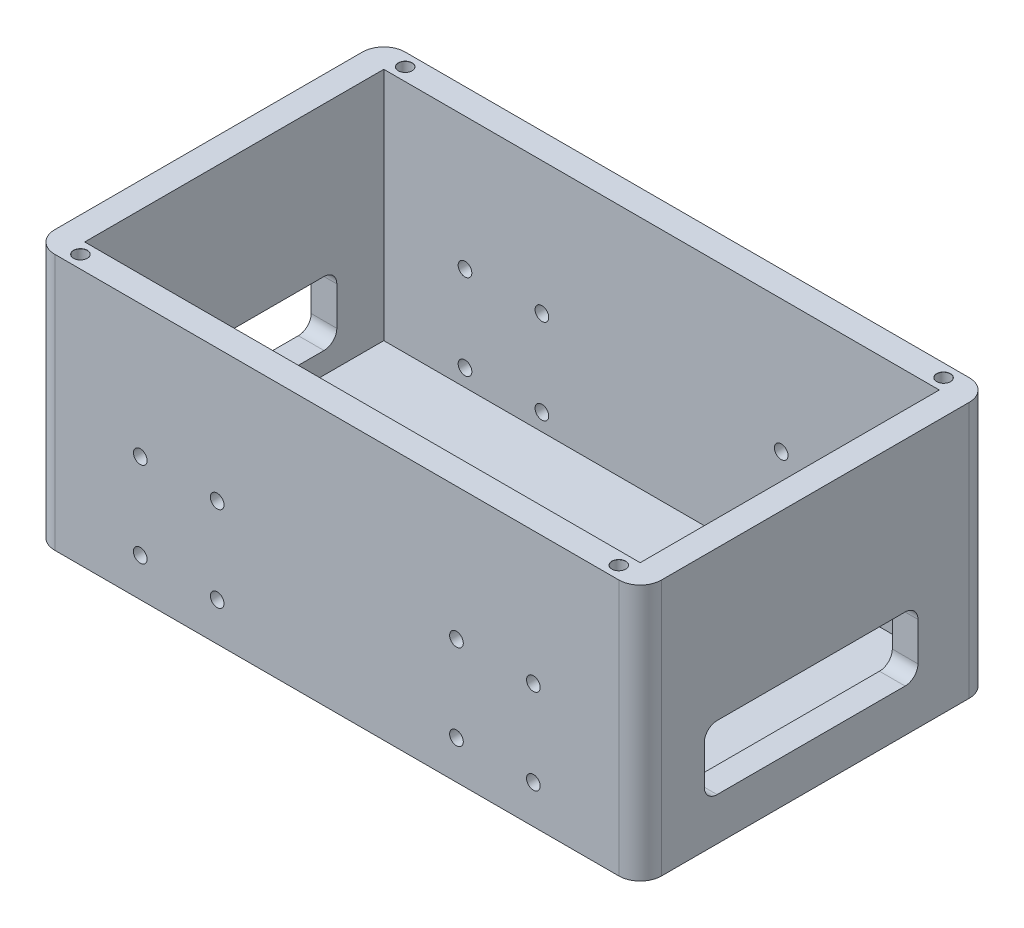
SolidWorks part; units mm, degrees
ref_plane "前视基准面" through (0, 0, 0) normal (0, 0, 1) x (1, 0, 0)
ref_plane "上视基准面" through (0, 0, 0) normal (0, 1, 0) x (1, 0, 0)
ref_plane "右视基准面" through (0, 0, 0) normal (1, 0, 0) x (0, 0, -1)
sketch "Sketch1" plane through (0, 0, 0) normal (0, 1, 0) x (1, 0, 0)
  line L1 (0, 0) -> (142, 0)
  line L2 (0, 0) -> (0, -82)
  line L3 (0, -82) -> (142, -82)
  line L4 (142, 0) -> (142, -82)
  dimension "D1" = 142
  dimension "D2" = 82
extrude "Boss-Extrude1" add sketch "Sketch1" along normal blind 60 contours L2 L1 L4 L3
sketch "Sketch2" plane through (0, 60, 0) normal (0, 1, 0) x (1, 0, 0)
  line L0 (0, -82) -> (142, -82) construction
  line L1 (6, -76) -> (136, -76)
  line L2 (6, -76) -> (6, -6)
  line L3 (6, -6) -> (136, -6)
  line L4 (136, -76) -> (136, -6)
  line L5 (6, -76) -> (136, -6) construction
  line L6 (6, -6) -> (136, -76) construction
  line L7 (142, 0) -> (142, -82) construction
  point P0 (71, -41)
  dimension "D1" = 130
  dimension "D2" = 70
  dimension "D3" = 6
  dimension "D4" = 6
extrude "Cut-Extrude1" cut sketch "Sketch2" against normal blind 55 contours L2 L1 L4 L3
hole_wizard "M3 Clearance Hole1" positions "Sketch3" profile "Sketch4" hole size "M3" standard "GB"
sketch "Sketch3" plane through (0, 5, 0) normal (0, 1, 0) x (1, 0, 0)
  line L3 (6, -6) -> (136, -6) construction
  line L4 (136, -76) -> (136, -6) construction
  point P0 (118.5, -17)
  point P2 (120, -65)
  point P4 (67.5, -32)
  point P6 (67.5, -60)
  dimension "D1" = 1.5
  dimension "D2" = 48
  dimension "D3" = 28
  dimension "D4" = 51
  dimension "D5" = 15
  dimension "D6" = 52.5
  dimension "D7" = 11
  dimension "D8" = 17.5
sketch "Sketch4" plane through (118.5, 5, 17) normal (1, 0, 0) x (0, 0, 1)
  line L0 (0, 0) -> (0, 5.9614)
  line L1 (0, 5.9614) -> (1.6, 5)
  line L2 (1.6, 5) -> (1.6, 0.025)
  line L3 (1.6, 0.025) -> (1.625, 0)
  line L5 (1.625, 0) -> (0, 0)
  line L6 (-1.6, 0.025) -> (-1.625, 0) construction
  line L10 (0, 5.9614) -> (-1.6, 5) construction
  line L11 (0, -6.35) -> (0, 107.95) construction
  dimension "Hole Dia." = 3.2
  dimension "Hole Depth" = 5
  dimension "Near C'Sink Dia." = 3.25
  dimension "Near C'Sink Angle" = 90
  dimension "Drill Angle" = 118
fillet "Fillet1" radius 5 4 edges at (142, 30, 82) (142, 30, 0) (0, 30, 0) (0, 30, 82)
sketch "Sketch9" plane through (142, 0, 0) normal (1, 0, 0) x (0, 0, -1)
  line L0 (-5, 0) -> (-77, 0) construction
  line L1 (-67, 25) -> (-17, 25)
  line L2 (-67, 25) -> (-67, 10)
  line L3 (-67, 10) -> (-17, 10)
  line L4 (-17, 25) -> (-17, 10)
  line L5 (-77, 60) -> (-77, 0) construction
  dimension "D1" = 50
  dimension "D2" = 15
  dimension "D3" = 10
  dimension "D4" = 10
extrude "Cut-Extrude4" cut sketch "Sketch9" against normal through all contours L2 L1 L4 L3
fillet "Fillet2" radius 3 8 edges at (3, 10, 67) (3, 25, 67) (3, 10, 17) (3, 25, 17) (139, 10, 17) (139, 25, 17) (139, 10, 67) (139, 25, 67)
hole_wizard "M3 Clearance Hole2" positions "Sketch10" profile "Sketch11" hole size "M3" standard "GB" end condition through all
sketch "Sketch10" plane through (0, 60, 0) normal (0, 1, 0) x (1, 0, 0)
  line L0 (0, -5) -> (0, -77) construction
  line L1 (5, 0) -> (137, 0) construction
  line L2 (5, -82) -> (137, -82) construction
  line L3 (142, -5) -> (142, -77) construction
  point P0 (8, -3)
  point P2 (8, -79)
  point P4 (134, -79)
  point P6 (134, -3)
  dimension "D1" = 8
  dimension "D2" = 3
  dimension "D3" = 8
  dimension "D4" = 3
  dimension "D5" = 3
  dimension "D6" = 8
  dimension "D7" = 8
  dimension "D8" = 3
sketch "Sketch11" plane through (8, 60, 3) normal (1, 0, 0) x (0, 0, 1)
  line L0 (0, 0) -> (0, 60)
  line L1 (0, 60) -> (1.6, 60)
  line L2 (1.6, 60) -> (1.6, 0.025)
  line L3 (1.6, 0.025) -> (1.625, 0)
  line L5 (1.625, 0) -> (0, 0)
  line L6 (-1.6, 0.025) -> (-1.625, 0) construction
  line L11 (0, -6.35) -> (0, 107.95) construction
  dimension "Thru Hole Dia." = 3.2
  dimension "Thru Hole Depth" = 60
  dimension "Near C'Sink Dia." = 3.25
  dimension "Near C'Sink Angle" = 90
hole_wizard "M3 Clearance Hole3" positions "Sketch12" profile "Sketch13" hole size "M3" standard "GB" end condition through all
sketch "Sketch12" plane through (0, 0, 0) normal (0, 0, -1) x (-1, 0, 0)
  line L1 (-137, 60) -> (-137, 0) construction
  line L2 (-71, 0) -> (-71, 69.9199) construction
  line L3 (-5, 0) -> (-137, 0) construction
  point P0 (-117, 29)
  point P2 (-99, 29)
  point P4 (-117, 9)
  point P6 (-99, 9)
  point P23 (-25, 9)
  point P24 (-43, 9)
  point P25 (-43, 29)
  point P26 (-25, 29)
  point P27 (-99, 9)
  point P28 (-43, 8.4979)
  point P29 (-43, 9)
  dimension "D1" = 18
  dimension "D2" = 20
  dimension "D3" = 9
  dimension "D4" = 20
  dimension "D5" = 20
  dimension "D6" = 20
  dimension "D7" = 18
sketch "Sketch13" plane through (117, 29, 0) normal (1, 0, 0) x (0, 1, 0)
  line L0 (0, 0) -> (0, 82)
  line L1 (0, 82) -> (1.6, 82)
  line L2 (1.6, 82) -> (1.6, 0.025)
  line L3 (1.6, 0.025) -> (1.625, 0)
  line L5 (1.625, 0) -> (0, 0)
  line L6 (-1.6, 0.025) -> (-1.625, 0) construction
  line L11 (0, -6.35) -> (0, 107.95) construction
  dimension "Thru Hole Dia." = 3.2
  dimension "Thru Hole Depth" = 82
  dimension "Near C'Sink Dia." = 3.25
  dimension "Near C'Sink Angle" = 90
